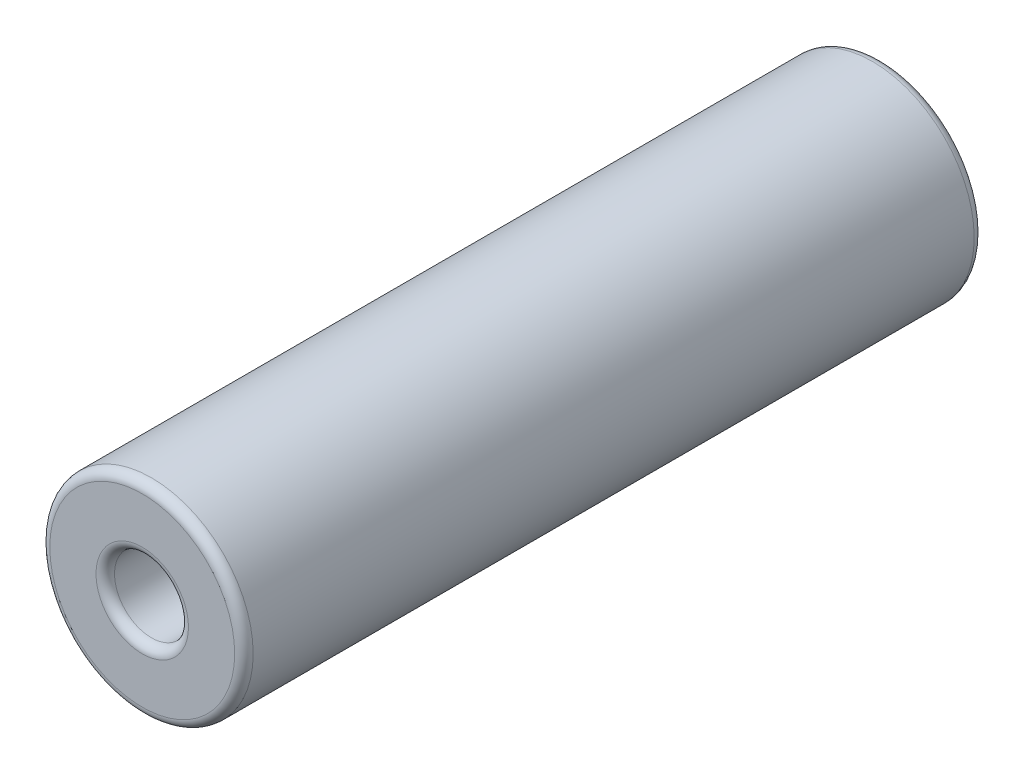
SolidWorks part; units mm, degrees
material "Cast Alloy Steel"
ref_plane "Front Plane" through (0, 0, 0) normal (0, 0, 1) x (1, 0, 0)
ref_plane "Top Plane" through (0, 0, 0) normal (0, 1, 0) x (1, 0, 0)
ref_plane "Right Plane" through (0, 0, 0) normal (1, 0, 0) x (0, 0, -1)
sketch "Sketch1" plane through (0, 0, 0) normal (0, 0, 1) x (1, 0, 0)
  circle A0 centre (0, 0) radius 5.5
  dimension "D1" = 11
extrude "Boss-Extrude1" add sketch "Sketch1" along normal blind 40
sketch "Sketch2" plane through (0, 0, 40) normal (0, 0, 1) x (1, 0, 0)
  circle A0 centre (0, 0) radius 2
extrude "Cut-Extrude1" cut sketch "Sketch2" against normal through all
fillet "Fillet1" radius 0.5 4 edges at (5.5, 0, 0) (2, 0, 0) (5.5, 0, 40) (2, 0, 40)
